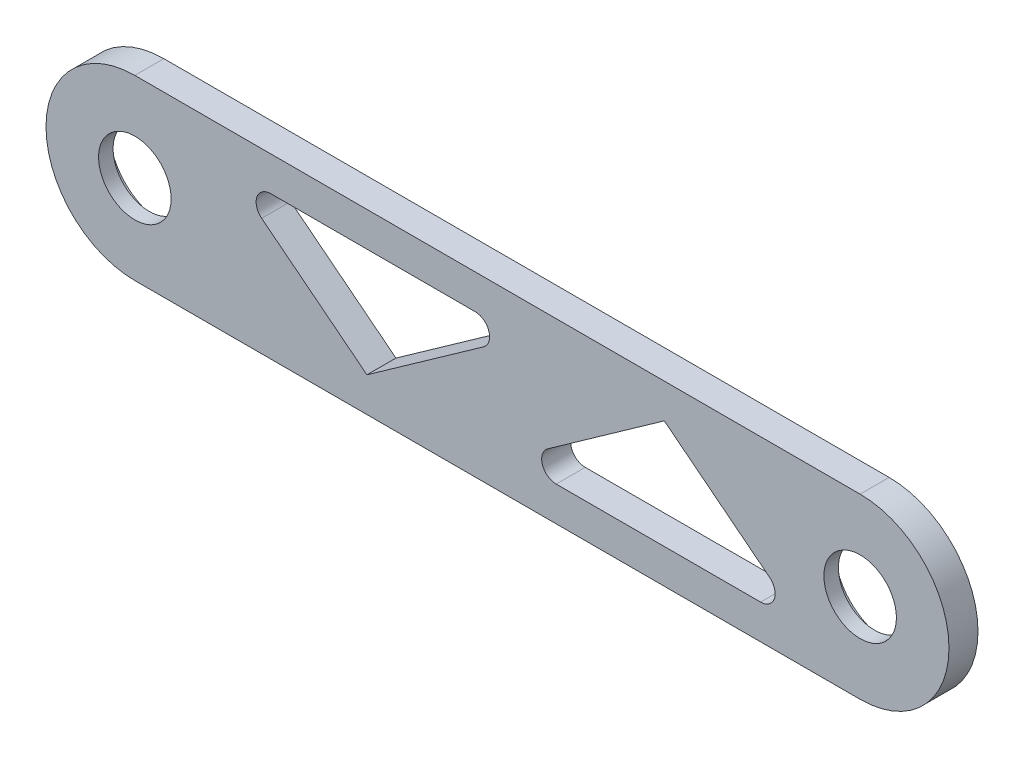
SolidWorks part; units mm, degrees
ref_plane "前视基准面" through (0, 0, 0) normal (0, 0, 1) x (1, 0, 0)
ref_plane "上视基准面" through (0, 0, 0) normal (0, 1, 0) x (1, 0, 0)
ref_plane "右视基准面" through (0, 0, 0) normal (1, 0, 0) x (0, 0, -1)
sketch "草图1" plane through (0, 0, 0) normal (0, 0, 1) x (1, 0, 0)
  line L0 (0, 12.25) -> (100, 12.25)
  line L1 (0, -12.25) -> (100, -12.25)
  arc A0 (0, 12.25) -> (0, -12.25) centre (0, 0) ccw
  arc A1 (100, -12.25) -> (100, 12.25) centre (100, 0) ccw
  circle A2 centre (0, 0) radius 5
  circle A10 centre (100, 0) radius 5
  point P20 (100, 0)
  dimension "D1" = 24.5
  dimension "D3" = 10
  dimension "D4" = 10
  dimension "D2" = 2
extrude "凸台-拉伸1" add sketch "草图1" along normal blind 4
ref_plane "基准面6" through (0, 0, 2) normal (0, 0, 1) x (1, 0, 0)
sketch "草图4" plane through (0, 0, 2) normal (0, 0, 1) x (1, 0, 0)
  circle A0 centre (0, 0) radius 7.5
  circle A1 centre (100, 0) radius 7.5
  dimension "D1" = 15
  dimension "D2" = 15
extrude "切除-拉伸3" cut sketch "草图4" against normal blind 3
sketch "草图5" plane through (0, 0, 0) normal (0, 0, -1) x (-1, 0, 0)
  line L0 (-100, 7.5) -> (-50, 7.5) construction
  line L1 (-100, -7.5) -> (-50, -7.5) construction
  line L2 (-100, 0) -> (0, 0) construction
  line L3 (-50, 7.5) -> (-50, -7.5) construction
  line L4 (-75, 7.5) -> (-75, -7.5) construction
  line L5 (-73, 7.5) -> (-87.5162, -3.9286)
  line L6 (-86.279, -7.5) -> (-58.0923, -7.5)
  line L7 (-56.937, -3.8674) -> (-73, 7.5)
  line L11 (-32, -7.5) -> (-17.4838, 3.9286)
  line L12 (-48.063, 3.8674) -> (-32, -7.5)
  line L13 (-18.721, 7.5) -> (-46.9077, 7.5)
  circle A0 centre (-100, 0) radius 7.5 construction
  circle A1 centre (-100, 0) radius 7.5 construction
  arc A4 (-18.721, 7.5) -> (-17.4838, 3.9286) centre (-18.721, 5.5) cw
  arc A5 (-46.9077, 7.5) -> (-48.063, 3.8674) centre (-46.9077, 5.5) ccw
  arc A6 (-58.0923, -7.5) -> (-56.937, -3.8674) centre (-58.0923, -5.5) ccw
  arc A7 (-86.279, -7.5) -> (-87.5162, -3.9286) centre (-86.279, -5.5) cw
  dimension "D1" = 2
extrude "切除-拉伸4" cut sketch "草图5" against normal up to next
